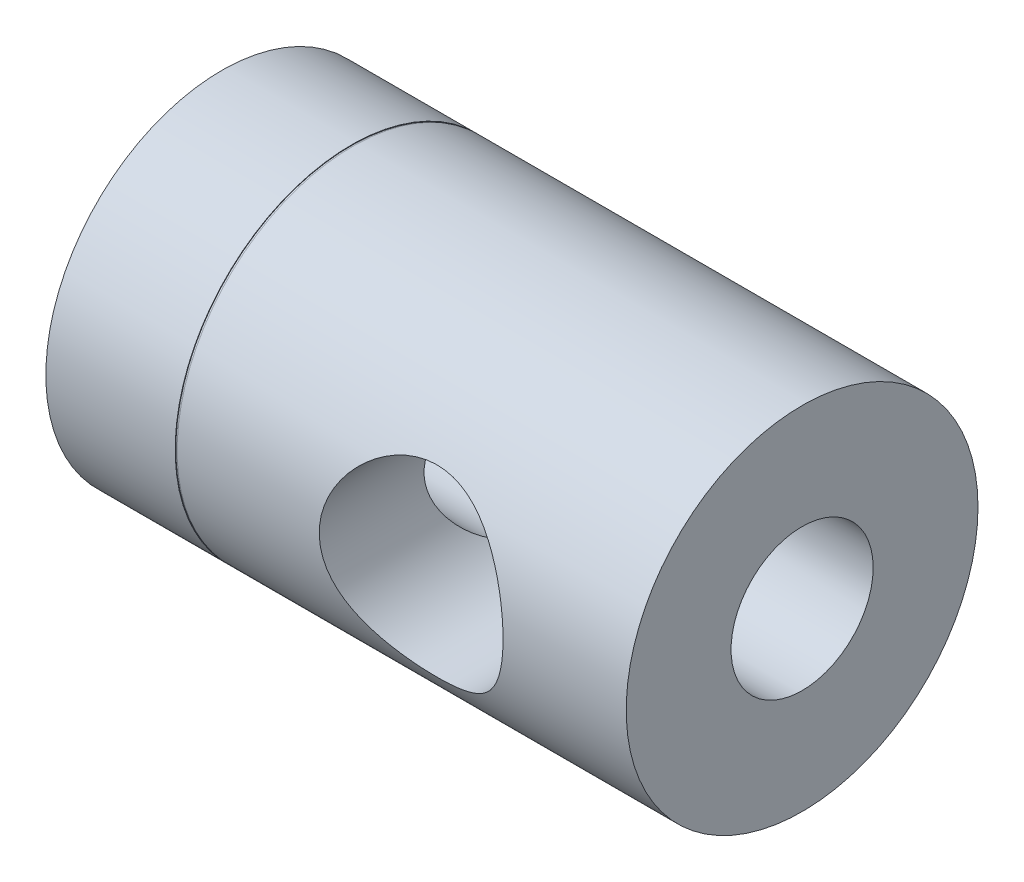
SolidWorks part; units mm, degrees
material "6061-T6 (SS)"
ref_plane "Front Plane" through (0, 0, 0) normal (0, 0, 1) x (1, 0, 0)
ref_plane "Top Plane" through (0, 0, 0) normal (0, 1, 0) x (1, 0, 0)
ref_plane "Right Plane" through (0, 0, 0) normal (1, 0, 0) x (0, 0, -1)
sketch "Sketch1" plane through (0, 0, 0) normal (0, 0, 1) x (1, 0, 0)
  line L0 (0, 0) -> (68.2535, 0) construction
  line L1 (0, 0) -> (-86.5654, 0) construction
  line L2 (-1.7145, 3.81) -> (15.6845, 3.81)
  line L3 (15.6845, 3.81) -> (15.6845, 9.4298)
  line L4 (15.6845, 9.4298) -> (-8.3947, 9.4297)
  line L5 (-1.7145, 3.81) -> (-19.1135, 3.81)
  line L6 (-15.4305, 9.4297) -> (-19.1135, 3.81)
  line L7 (-8.4455, 9.398) -> (-8.3947, 9.398)
  line L8 (-8.4963, 9.4297) -> (-15.4305, 9.4297)
  line L9 (-8.4455, 9.398) -> (-8.4963, 9.398)
  line L10 (-8.3947, 9.398) -> (-8.3947, 9.4297)
  line L11 (-8.4963, 9.398) -> (-8.4963, 9.4297)
  dimension "D1" = 3.81
  dimension "D2" = 9.4298
  dimension "D3" = 17.399
  dimension "D4" = 17.399
  dimension "D5" = 31.115
revolve "Revolve1" add sketch "Sketch1" angle 360 about L1
sketch "Sketch2" plane through (0, 0, 0) normal (0, 0, 1) x (1, 0, 0)
  line L0 (15.6845, 0) -> (4.1529, 0) construction
  line L1 (15.6845, -9.4298) -> (15.6845, 9.4298) construction
  circle A0 centre (4.1529, 0) radius 4.9276
  dimension "D2" = 9.8552
  dimension "D1" = 11.5316
extrude "Cut-Extrude1" cut sketch "Sketch2" against normal through all and the other way through all
